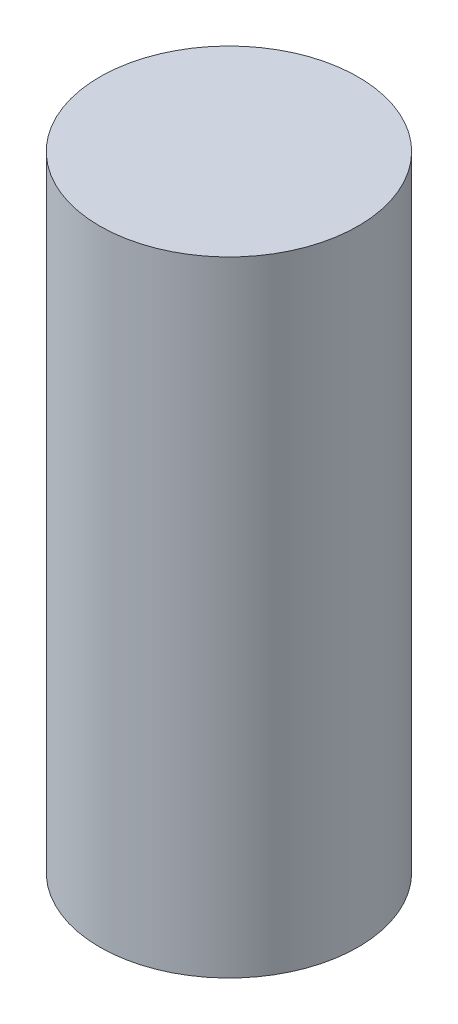
SolidWorks part; units mm, degrees
ref_plane "Front Plane" through (0, 0, 0) normal (0, 0, 1) x (1, 0, 0)
ref_plane "Top Plane" through (0, 0, 0) normal (0, 1, 0) x (1, 0, 0)
ref_plane "Right Plane" through (0, 0, 0) normal (1, 0, 0) x (0, 0, -1)
sketch "Sketch1" plane through (0, 0, 0) normal (0, 1, 0) x (1, 0, 0)
  circle A0 centre (0, 0) radius 6
  dimension "D1" = 12
extrude "Boss-Extrude1" add sketch "Sketch1" along normal mid plane 29
